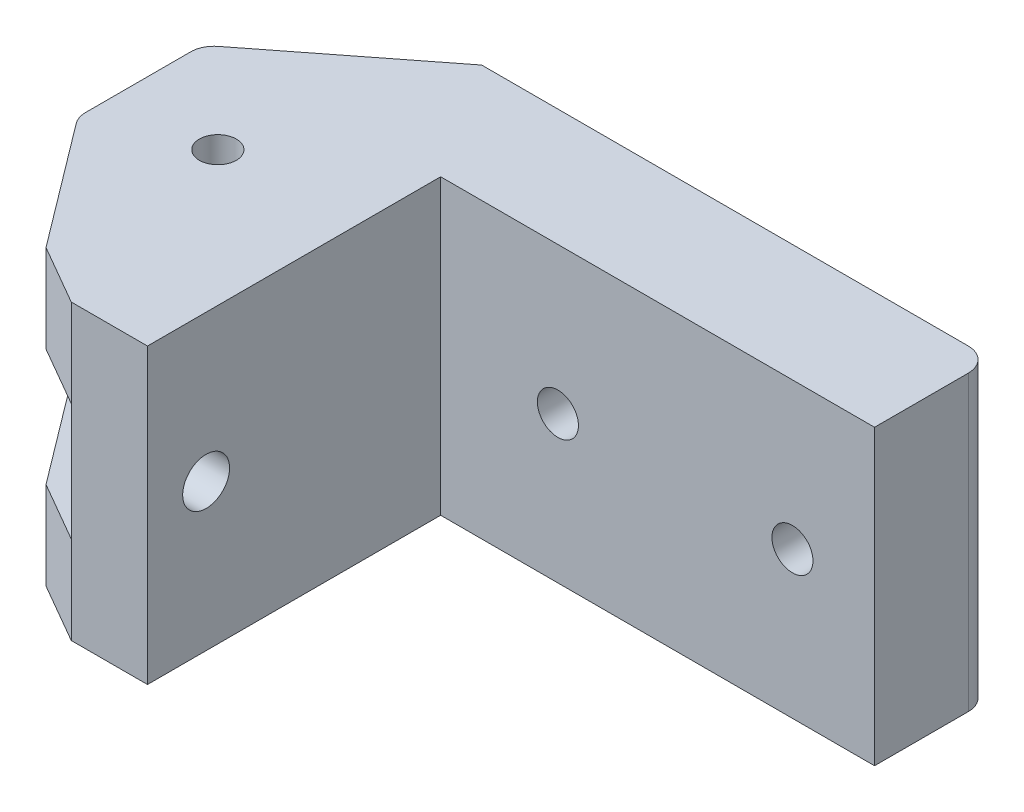
SolidWorks part; units mm, degrees
ref_plane "Front Plane" through (0, 0, 0) normal (0, 0, 1) x (1, 0, 0)
ref_plane "Top Plane" through (0, 0, 0) normal (0, 1, 0) x (1, 0, 0)
ref_plane "Right Plane" through (0, 0, 0) normal (1, 0, 0) x (0, 0, -1)
sketch "Sketch1" plane through (0, 0, 0) normal (0, 1, 0) x (1, 0, 0)
  line L0 (0, 0) -> (-43.5, 0)
  line L1 (-43.5, 0) -> (-43.5, -35) construction
  line L2 (-43.5, -35) -> (-37, -35)
  line L3 (-37, -35) -> (-37, -10)
  line L4 (-37, -10) -> (0, -10)
  line L5 (0, -10) -> (0, 0)
  line L6 (-43.5, 0) -> (-56.8853, -10.4577)
  line L7 (-56.8853, -10.4577) -> (-56.8853, -21.0577)
  line L8 (-56.8853, -21.0577) -> (-48.5962, -32.0577)
  line L9 (-48.5962, -32.0577) -> (-43.5, -35)
  line L10 (-43.5, -17.5) -> (-48.5, -17.5) construction
  circle A0 centre (-48.5, -17.5) radius 1.575
  dimension "D11" = 3.15
  dimension "D1" = 43.5
  dimension "D2" = 35
  dimension "D3" = 10
  dimension "D4" = 37
  dimension "D5" = 30
  dimension "D6" = 38
  dimension "D7" = 10.6
  dimension "D8" = 37
  dimension "D9" = 11
  dimension "D10" = 5
extrude "Boss-Extrude1" add sketch "Sketch1" along normal mid plane 25
sketch "Sketch2" plane through (0, 0, 35) normal (0, 0, 1) x (1, 0, 0)
  line L0 (-43.5, 12.5) -> (-43.5, -12.5) construction
  line L1 (-43.5, -5) -> (-56.8853, -5)
  line L2 (-43.5, -5) -> (-43.5, 5)
  line L3 (-43.5, 5) -> (-56.8853, 5)
  line L4 (-56.8853, -5) -> (-56.8853, 5)
  line L5 (-56.8853, 12.5) -> (-56.8853, -12.5) construction
  line L6 (-56.8853, 12.5) -> (-48.5962, 12.5) construction
  dimension "D1" = 7.5
  dimension "D2" = 10
extrude "Cut-Extrude1" cut sketch "Sketch2" against normal through all
sketch "Sketch3" plane through (0, 0, 10) normal (0, 0, 1) x (1, 0, 0)
  line L1 (0, 0) -> (-27, 0) construction
  line L2 (-37, 12.5) -> (-37, -12.5) construction
  circle A0 centre (-27, 0) radius 1.75
  circle A1 centre (-7, 0) radius 1.75
  dimension "D1" = 3.5
  dimension "D2" = 20
  dimension "D3" = 10
extrude "Cut-Extrude2" cut sketch "Sketch3" against normal blind 25
sketch "Sketch4" plane through (0, 0, 0) normal (0, 0, -1) x (-1, 0, 0)
  circle A0 centre (7, 0) radius 4
  circle A2 centre (27, 0) radius 4
extrude "Cut-Extrude3" cut sketch "Sketch4" against normal blind 4
fillet "Fillet1" radius 2 5 edges at (0, 0, 0) (-56.8853, 8.75, 10.4577) (-56.8853, 8.75, 21.0577) (-56.8853, -8.75, 21.0577) (-56.8853, -8.75, 10.4577)
sketch "Sketch5" plane through (-43.5, 0, 0) normal (-1, 0, 0) x (0, 0, 1)
  line L0 (30, -12.5) -> (30, 12.5) construction
  line L3 (35, -5) -> (35, 5) construction
  line L4 (21.5922, 12.5) -> (32.0577, 12.5) construction
  line L5 (21.5922, -12.5) -> (32.0577, -12.5) construction
  circle A0 centre (30, 0) radius 2
  dimension "D1" = 4
  dimension "D2" = 5
sketch "Sketch6" plane through (0, 12.5, 0) normal (0, 1, 0) x (1, 0, 0)
  line L0 (-37, -35) -> (-37, -10)
extrude "Cut-Extrude4" cut sketch "Sketch5" against normal blind 10
sketch "Sketch7" plane through (-43.5, 0, 0) normal (-1, 0, 0) x (0, 0, 1)
  circle A0 centre (30, 0) radius 3.575
  dimension "D1" = 7.15
extrude "Cut-Extrude5" cut sketch "Sketch7" against normal blind 3.5
ref_plane "Plane1" through (0, 0, 0) normal (0, 1, 0) x (1, 0, 0)
sketch "Sketch8" plane through (0, 0, 0) normal (0, 1, 0) x (1, 0, 0)
  circle A0 centre (-48.5, -17.5) radius 10
extrude "Cut-Extrude6" cut sketch "Sketch8" against normal blind 5 and the other way blind 5
sketch "Sketch9" plane through (0, -12.5, 0) normal (0, -1, 0) x (1, 0, 0)
  line L1 (-46.8006, 14.4814) -> (-45.0361, 17.4624)
  line L2 (-45.0361, 17.4624) -> (-46.7355, 20.481)
  line L3 (-46.7355, 20.481) -> (-50.1994, 20.5186)
  line L4 (-50.1994, 20.5186) -> (-51.9639, 17.5376)
  line L5 (-51.9639, 17.5376) -> (-50.2645, 14.519)
  line L6 (-50.2645, 14.519) -> (-46.8006, 14.4814)
  circle A0 centre (-48.5, 17.5) radius 3 construction
extrude "Cut-Extrude7" cut sketch "Sketch9" against normal blind 3 contours L6 L1 L2 L3 L4 L5
